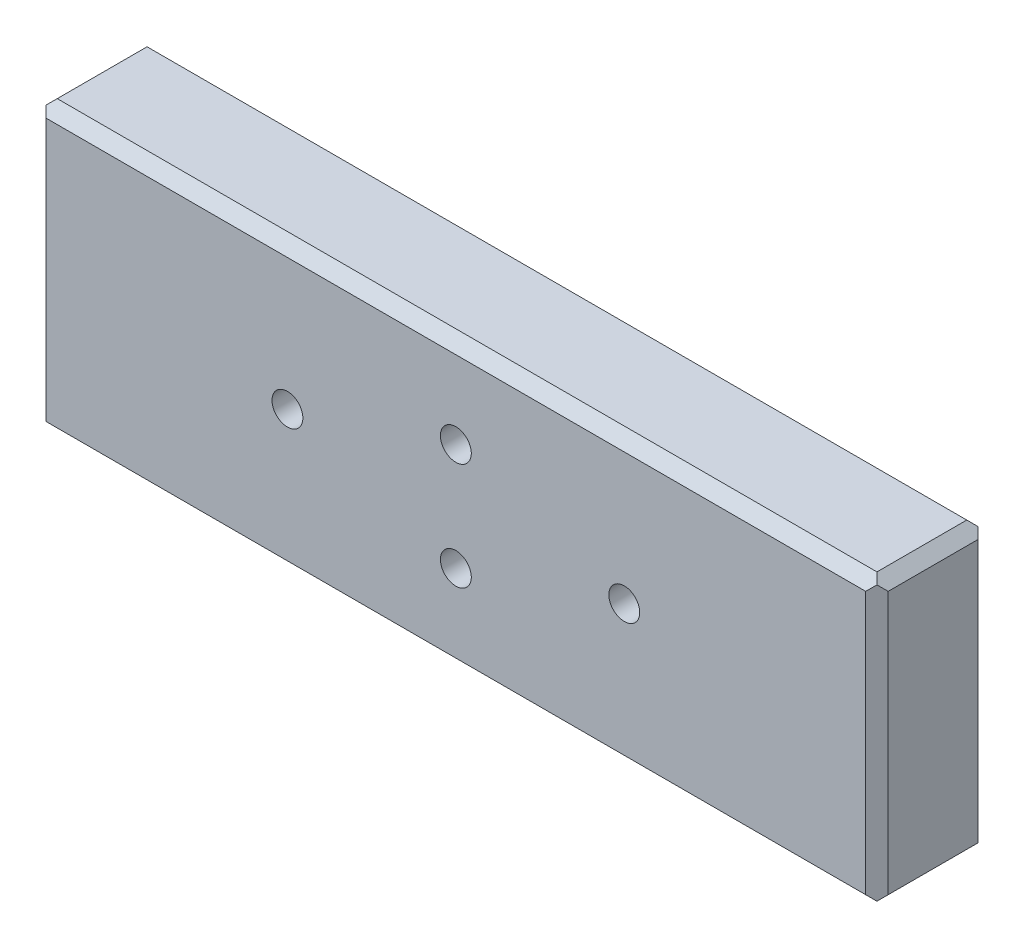
SolidWorks part; units mm, degrees
material "6063-T5"
ref_plane "Alzado" through (0, 0, 0) normal (0, 0, 1) x (1, 0, 0)
ref_plane "Planta" through (0, 0, 0) normal (0, 1, 0) x (1, 0, 0)
ref_plane "Vista lateral" through (0, 0, 0) normal (1, 0, 0) x (0, 0, -1)
sketch "Croquis1" plane through (0, 0, 0) normal (0, 0, 1) x (1, 0, 0)
  line L1 (-75, 25.4) -> (75, 25.4)
  line L2 (-75, 25.4) -> (-75, -25.4)
  line L3 (-75, -25.4) -> (75, -25.4)
  line L4 (75, 25.4) -> (75, -25.4)
  line L5 (-75, 25.4) -> (75, -25.4) construction
  line L6 (-75, -25.4) -> (75, 25.4) construction
  point P0 (0, 0)
  dimension "D1" = 50.8
  dimension "D2" = 150
extrude "Saliente-Extruir1" add sketch "Croquis1" along normal blind 20
sketch "Croquis2" plane through (0, 0, 0) normal (0, 0, -1) x (-1, 0, 0)
  line L0 (-75, 0) -> (75, 0) construction
  line L1 (-75, -25.4) -> (-75, 25.4) construction
  line L2 (75, 25.4) -> (75, -25.4) construction
  line L3 (0, 25.4) -> (0, -25.4) construction
  line L4 (-75, 25.4) -> (75, 25.4) construction
  line L5 (75, -25.4) -> (-75, -25.4) construction
  circle A0 centre (0, 9.55) radius 2.75
  circle A1 centre (0, -9.55) radius 2.75
  circle A2 centre (30, 0) radius 2.75
  circle A3 centre (-30, 0) radius 2.75
  dimension "D1" = 5.5
  dimension "D4" = 5.5
  dimension "D5" = 30
  dimension "D2" = 19.1
  dimension "D3" = 9.55
  dimension "D6" = 60
extrude "Cortar-Extruir1" cut sketch "Croquis2" against normal through all
sketch "Croquis3" plane through (0, 0, 0) normal (0, 0, -1) x (-1, 0, 0)
  line L0 (0, 25.4) -> (0, -25.4) construction
  line L1 (-75, 25.4) -> (75, 25.4) construction
  line L2 (75, -25.4) -> (-75, -25.4) construction
  circle A0 centre (0, 9.55) radius 5
  circle A1 centre (0, -9.55) radius 5
  dimension "D1" = 10
extrude "Cortar-Extruir2" cut sketch "Croquis3" against normal blind 5
chamfer "Chaflán1" distance 2 angle 45 4 edges at (-75, 0, 0) (0, -25.4, 0) (75, 0, 0) (0, 25.4, 0)
chamfer "Chaflán2" distance 2 angle 45 4 edges at (-75, 0, 20) (0, 25.4, 20) (75, 0, 20) (0, -25.4, 20)
chamfer "Chaflán3" distance 2 angle 45 4 edges at (75, 25.4, 10) (-75, 25.4, 10) (-75, -25.4, 10) (75, -25.4, 10)
